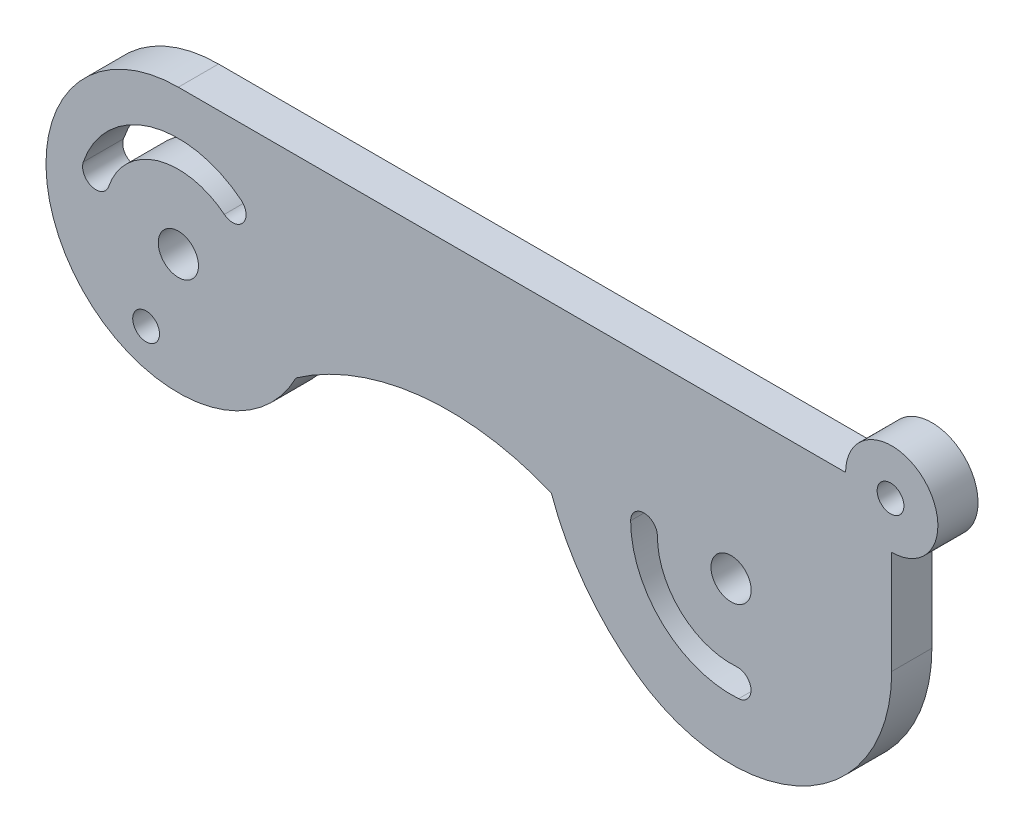
SolidWorks part; units mm, degrees
material "Acrylic (Medium-high impact)"
ref_plane "Front Plane" through (0, 0, 0) normal (0, 0, 1) x (1, 0, 0)
ref_plane "Top Plane" through (0, 0, 0) normal (0, 1, 0) x (1, 0, 0)
ref_plane "Right Plane" through (0, 0, 0) normal (1, 0, 0) x (0, 0, -1)
sketch "Sketch1" plane through (0, 0, 0) normal (0, 0, 1) x (1, 0, 0)
  line L2 (56.4891, -2.8077) -> (56.4891, -10.5118)
  line L3 (3.209, -10.1693) -> (3.209, -0.6693) construction
  line L4 (3.209, -10.1693) -> (7.2662, -5.091) construction
  line L5 (44.4891, -10.5118) -> (44.4891, -26.8814) construction
  line L6 (44.4891, -10.1693) -> (45.4865, -24.028) construction
  line L7 (53.0429, 0.6385) -> (3.209, 0.6385)
  line L8 (3.209, -0.6693) -> (3.209, 0.6385) construction
  arc A1 (12.0011, -13.7677) -> (31.0638, -11.6768) centre (23.4461, -30.1693) cw
  circle A6 centre (56.3987, 0.6385) radius 1
  arc A16 (31.0638, -11.6768) -> (37.4039, -20.1968) centre (48.0317, -5.6693) ccw
  arc A17 (37.4039, -20.1968) -> (56.4891, -10.5118) centre (44.4891, -10.5118) ccw
  circle A23 centre (44.4891, -10.5118) radius 1.5
  circle A24 centre (3.209, -10.1693) radius 1.5
  arc A25 (38.9891, -10.5118) -> (44.9046, -15.9961) centre (44.4891, -10.5118) ccw
  arc A26 (36.9891, -10.5118) -> (45.0558, -17.9904) centre (44.4891, -10.5118) ccw
  arc A29 (6.642, -5.8723) -> (-1.9971, -8.3954) centre (3.209, -10.1693) ccw
  arc A30 (7.8903, -4.3097) -> (-3.8902, -7.7503) centre (3.209, -10.1693) ccw
  arc A32 (-3.8902, -7.7503) -> (-1.9971, -8.3954) centre (-2.9437, -8.0729) ccw
  arc A34 (44.9046, -15.9961) -> (45.0558, -17.9904) centre (44.9802, -16.9932) cw
  arc A35 (7.8903, -4.3097) -> (6.642, -5.8723) centre (7.2662, -5.091) cw
  arc A36 (38.9891, -10.5118) -> (36.9891, -10.5118) centre (37.9891, -10.5118) ccw
  arc A37 (56.4891, -2.8077) -> (53.0429, 0.6385) centre (56.4891, 0.6385) ccw
  arc A38 (3.209, 0.6385) -> (12.0011, -13.7677) centre (3.209, -9.2475) ccw
  dimension "D2" = 12
  dimension "D3" = 20
  dimension "D5" = 20
  dimension "D11" = 4
  dimension "D13" = 2
  dimension "D14" = 2
  dimension "D12" = 2
  dimension "D15" = 2
  dimension "D16" = 4
  dimension "D8" = 18
  dimension "D9" = 3
  dimension "D10" = 2
  dimension "D17" = 4.116
  dimension "D19" = 1
  dimension "D20" = 11
  dimension "D21" = 38.622
  dimension "D18" = 9
extrude "Boss-Extrude1" add sketch "Sketch1" along normal blind 3
sketch "Sketch2" plane through (0, 0, 3) normal (0, 0, 1) x (1, 0, 0)
  circle A0 centre (0.8016, -16.0354) radius 1
  dimension "D1" = 2
extrude "Cut-Extrude1" cut sketch "Sketch2" against normal blind 10 contours A0
